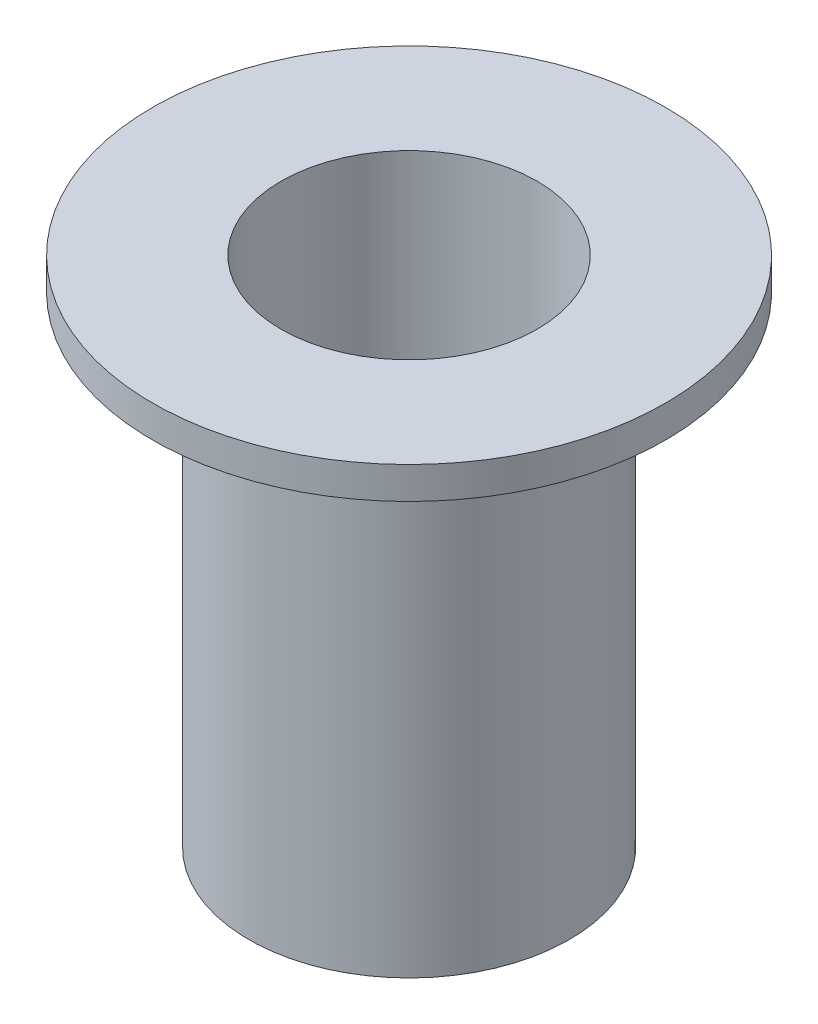
SolidWorks part; units mm, degrees
ref_plane "Front Plane" through (0, 0, 0) normal (0, 0, 1) x (1, 0, 0)
ref_plane "Top Plane" through (0, 0, 0) normal (0, 1, 0) x (1, 0, 0)
ref_plane "Right Plane" through (0, 0, 0) normal (1, 0, 0) x (0, 0, -1)
sketch "Sketch1" plane through (0, 0, 0) normal (1, 0, 0) x (0, 0, -1)
  line L0 (0, 0) -> (0, 54.003) construction
  line L1 (3.175, 0) -> (3.175, 12.7)
  line L2 (3.175, 12.7) -> (6.35, 12.7)
  line L3 (6.35, 12.7) -> (6.35, 11.9062)
  line L4 (6.35, 11.9062) -> (3.9688, 11.9062)
  line L5 (3.9688, 11.9062) -> (3.9688, 0)
  line L6 (3.9688, 0) -> (3.175, 0)
  dimension "D1" = 6.35
  dimension "D2" = 7.9375
  dimension "D3" = 12.7
  dimension "D4" = 12.7
  dimension "D5" = 0.7937
revolve "Revolve1" add sketch "Sketch1" angle 360 about L0
